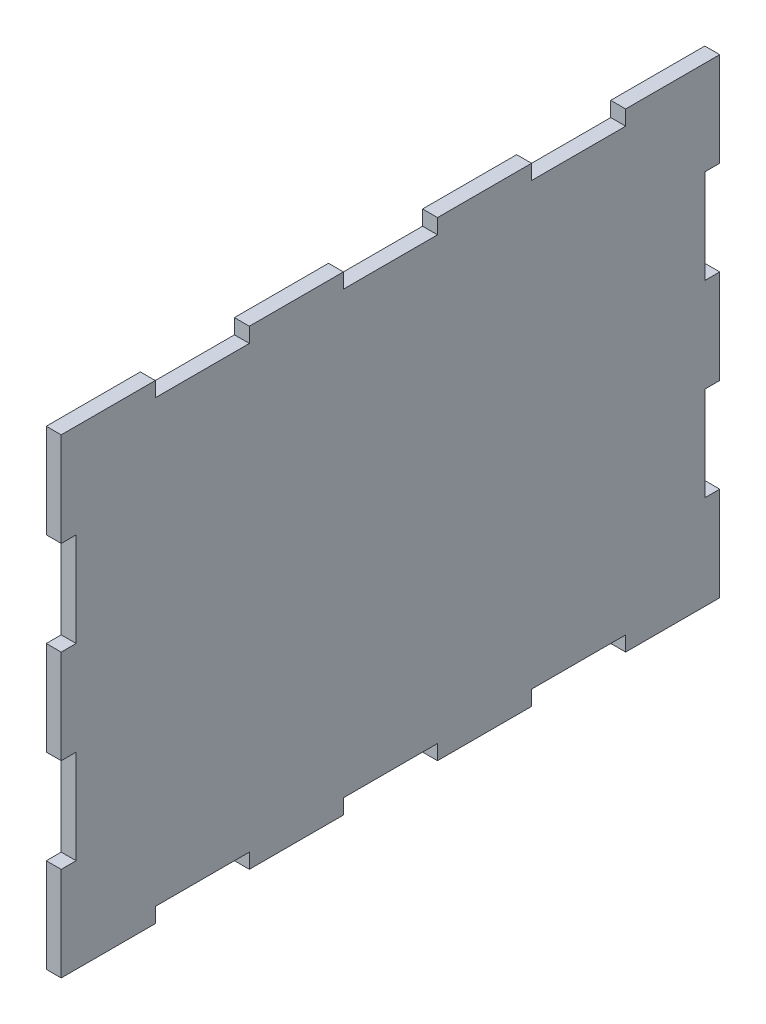
SolidWorks part; units mm, degrees
material "Acrylic (Medium-high impact)"
ref_plane "Front Plane" through (0, 0, 0) normal (0, 0, 1) x (1, 0, 0)
ref_plane "Top Plane" through (0, 0, 0) normal (0, 1, 0) x (1, 0, 0)
ref_plane "Right Plane" through (0, 0, 0) normal (1, 0, 0) x (0, 0, -1)
sketch "Sketch43" plane through (0, 0, 0) normal (1, 0, 0) x (0, 0, -1)
  line L3 (-738.1019, -49.9999) -> (-598.1019, -49.9999)
  line L4 (-738.1019, -49.9999) -> (-738.1019, 50)
  line L5 (-738.1019, 50) -> (-598.1019, 50)
  line L6 (-598.1019, -49.9999) -> (-598.1019, 50)
extrude "Boss-Extrude10" add sketch "Sketch43" along normal blind 3.175 separate body
sketch "Sketch45" plane through (3.175, 0, 0) normal (1, 0, 0) x (0, 0, -1)
  line L9 (-598.1019, 10.0001) -> (-598.1019, 30.0001)
  line L10 (-598.1019, -49.9999) -> (-598.1019, 50) construction
  line L11 (-598.1019, 10.0001) -> (-601.2769, 10.0001)
  line L12 (-601.2769, 10.0001) -> (-601.2769, 30.0001)
  line L13 (-738.1019, 10.0001) -> (-738.1019, 30.0001)
  line L14 (-738.1019, 50) -> (-738.1019, -49.9999) construction
  line L15 (-738.1019, 10.0001) -> (-734.9269, 10.0001)
  line L16 (-734.9269, 10.0001) -> (-734.9269, 30.0001)
  line L17 (-738.1019, 30.0001) -> (-734.9269, 30.0001)
  line L18 (-738.1019, -29.9999) -> (-734.9269, -29.9999)
  line L19 (-738.1019, -29.9999) -> (-738.1019, -9.9999)
  line L20 (-738.1019, -9.9999) -> (-734.9269, -9.9999)
  line L21 (-734.9269, -29.9999) -> (-734.9269, -9.9999)
  line L22 (-598.1019, -29.9999) -> (-601.2769, -29.9999)
  line L23 (-598.1019, -29.9999) -> (-598.1019, -9.9999)
  line L24 (-598.1019, -9.9999) -> (-601.2769, -9.9999)
  line L25 (-601.2769, -29.9999) -> (-601.2769, -9.9999)
  line L26 (-598.1019, 30.0001) -> (-601.2769, 30.0001)
  line L27 (-678.1019, -49.9999) -> (-678.1019, -46.8249)
  line L28 (-738.1019, -49.9999) -> (-598.1019, -49.9999) construction
  line L29 (-678.1019, -49.9999) -> (-658.1019, -49.9999)
  line L30 (-658.1019, -49.9999) -> (-658.1019, -46.8249)
  line L31 (-718.1019, -49.9999) -> (-698.1019, -49.9999)
  line L32 (-718.1019, -49.9999) -> (-718.1019, -46.8249)
  line L33 (-718.1019, -46.8249) -> (-698.1019, -46.8249)
  line L34 (-698.1019, -49.9999) -> (-698.1019, -46.8249)
  line L35 (-678.1019, -46.8249) -> (-658.1019, -46.8249)
  line L36 (-638.1019, -49.9999) -> (-638.1019, -46.8249)
  line L37 (-638.1019, -49.9999) -> (-618.1019, -49.9999)
  line L38 (-618.1019, -49.9999) -> (-618.1019, -46.8249)
  line L39 (-638.1019, -46.8249) -> (-618.1019, -46.8249)
  line L40 (-678.1019, 50) -> (-678.1019, 46.825)
  line L41 (-598.1019, 50) -> (-738.1019, 50) construction
  line L42 (-678.1019, 50) -> (-658.1019, 50)
  line L43 (-658.1019, 50) -> (-658.1019, 46.825)
  line L44 (-718.1019, 50) -> (-698.1019, 50)
  line L45 (-718.1019, 50) -> (-718.1019, 46.825)
  line L46 (-718.1019, 46.825) -> (-698.1019, 46.825)
  line L47 (-698.1019, 50) -> (-698.1019, 46.825)
  line L48 (-678.1019, 46.825) -> (-658.1019, 46.825)
  line L49 (-638.1019, 50) -> (-638.1019, 46.825)
  line L50 (-638.1019, 50) -> (-618.1019, 50)
  line L51 (-618.1019, 50) -> (-618.1019, 46.825)
  line L52 (-638.1019, 46.825) -> (-618.1019, 46.825)
  dimension "D1" = 2
  dimension "D2" = 2
  dimension "D3" = 3
  dimension "D4" = 3
extrude "Cut-Extrude22" cut sketch "Sketch45" against normal blind 3.175
